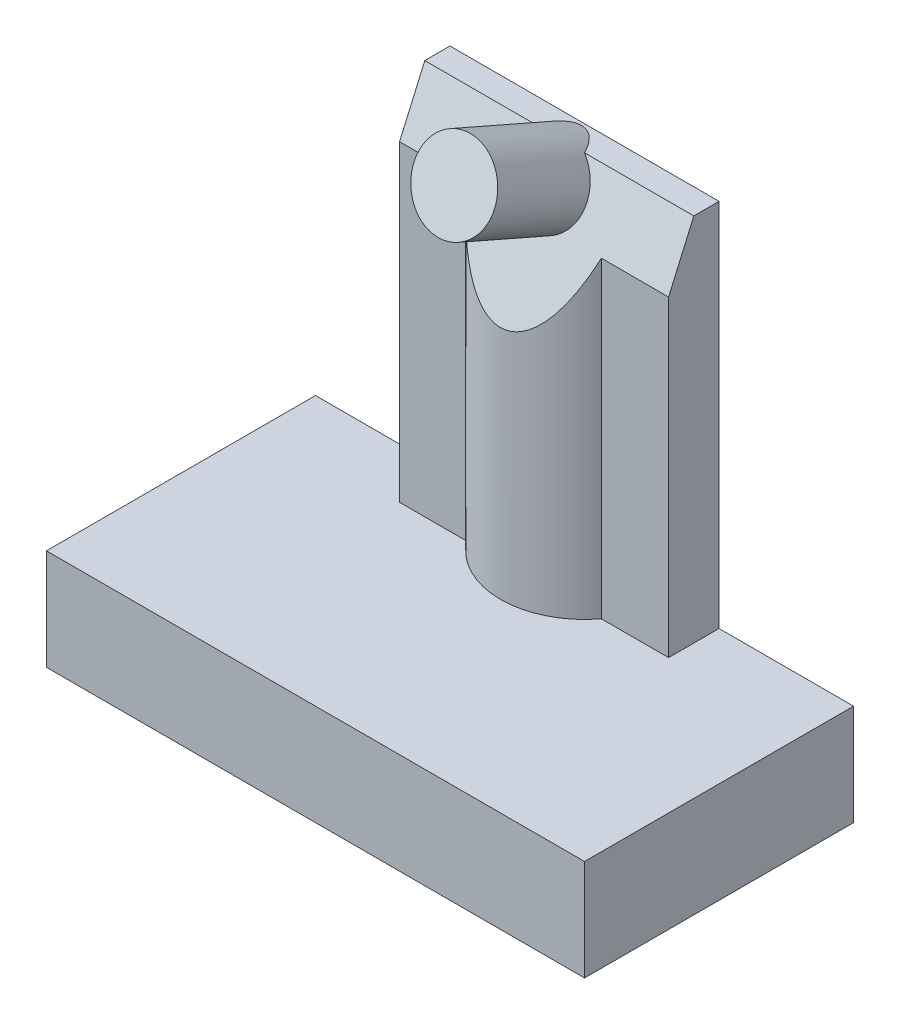
SolidWorks part; units mm, degrees
ref_plane "Front Plane" through (0, 0, 0) normal (0, 0, 1) x (1, 0, 0)
ref_plane "Top Plane" through (0, 0, 0) normal (0, 1, 0) x (1, 0, 0)
ref_plane "Right Plane" through (0, 0, 0) normal (1, 0, 0) x (0, 0, -1)
sketch "Sketch1" plane through (0, 0, 0) normal (0, 1, 0) x (1, 0, 0)
  line L1 (8, -4) -> (-8, -4)
  line L2 (8, -4) -> (8, 4)
  line L3 (8, 4) -> (-8, 4)
  line L4 (-8, -4) -> (-8, 4)
  line L5 (8, -4) -> (-8, 4) construction
  line L6 (8, 4) -> (-8, -4) construction
  point P0 (0, 0)
  dimension "D1" = 16
  dimension "D2" = 8
extrude "Boss-Extrude1" add sketch "Sketch1" along normal blind 3
shell "Shell1" thickness 1
sketch "Sketch2" plane through (0, 3, 0) normal (0, 1, 0) x (1, 0, 0)
  line L0 (-4, 4) -> (4, 4)
  line L1 (8, 4) -> (-8, 4) construction
  line L2 (4, 4) -> (4, 2.5)
  line L3 (4, 2.5) -> (2, 2.5)
  line L4 (0, 4) -> (0, -1.1137) construction
  line L5 (-4, 4) -> (-4, 2.5)
  line L6 (-4, 2.5) -> (-2, 2.5)
  arc A0 (-2, 2.5) -> (2, 2.5) centre (0, 4) ccw
  dimension "D1" = 4
  dimension "D2" = 1.5
extrude "Boss-Extrude2" add sketch "Sketch2" along normal blind 11 contours L3 A0 L6 L5 L0 L2
sketch "Sketch3" plane through (4, 0, 0) normal (1, 0, 0) x (0, 0, -1)
  line L0 (1.5, 14) -> (1.5, 10)
  line L1 (1.5, 14) -> (1.5, 3) construction
  line L2 (1.5, 14) -> (3.25, 14)
  line L3 (4, 14) -> (2.5, 14) construction
  line L4 (3.25, 14) -> (1.5, 10)
  dimension "D1" = 4
  dimension "D2" = 1.75
extrude "Cut-Extrude1" cut sketch "Sketch3" against normal through all
sketch "Sketch4" plane through (0, 1.0557, 2.4131) normal (0, 0.4008, 0.9162) x (1, 0, 0)
  line L0 (-4, 14.4295) -> (4, 14.4295) construction
  circle A0 centre (0, 13.1935) radius 1.2
  dimension "D1" = 2.4
  dimension "D2" = 1.236
extrude "Boss-Extrude3" add sketch "Sketch4" along normal blind 3 and the other way up to next
